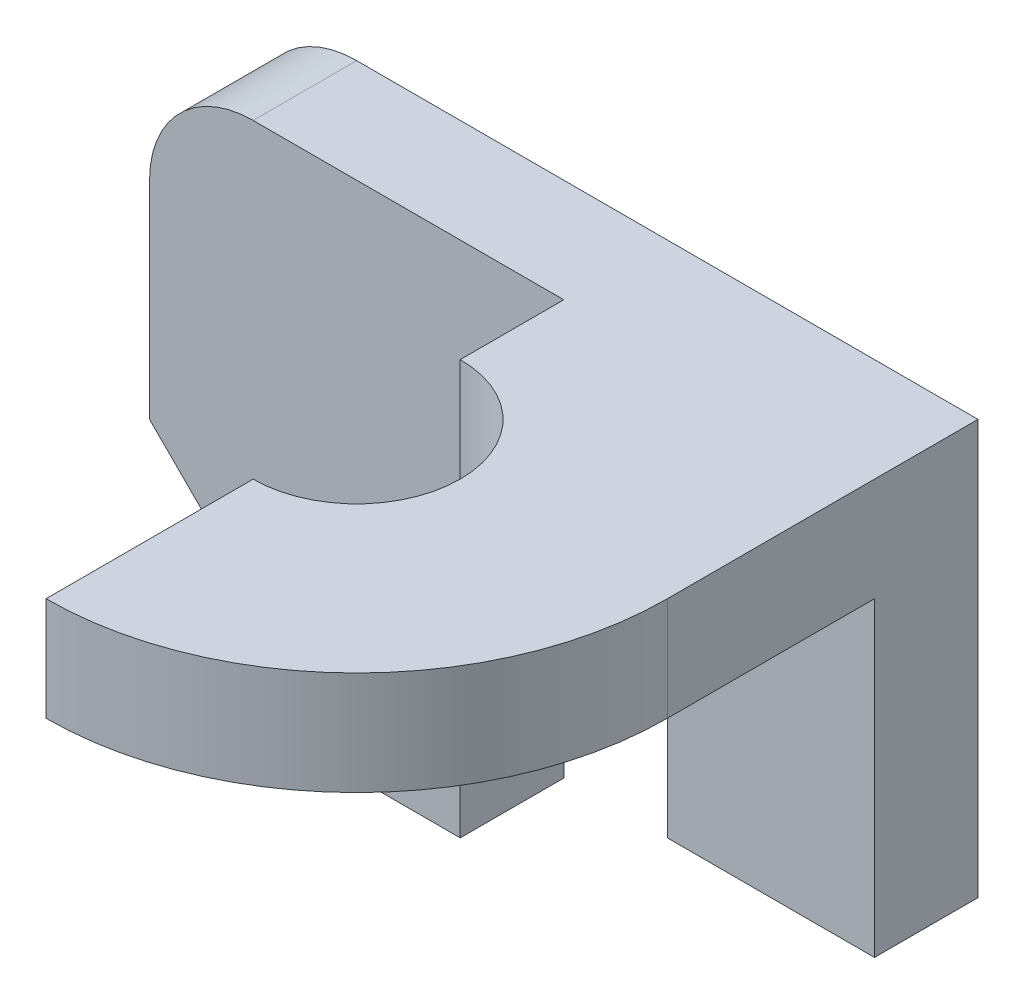
SolidWorks part; units mm, degrees
ref_plane "Front Plane" through (0, 0, 0) normal (0, 0, 1) x (1, 0, 0)
ref_plane "Top Plane" through (0, 0, 0) normal (0, 1, 0) x (1, 0, 0)
ref_plane "Right Plane" through (0, 0, 0) normal (1, 0, 0) x (0, 0, -1)
sketch "Sketch1" plane through (0, 0, 0) normal (0, 0, 1) x (1, 0, 0)
  line L0 (0, 0) -> (2, 0)
  line L1 (2, 0) -> (2, 4)
  line L2 (2, 4) -> (-4, 4)
  line L3 (-5, 3) -> (-5, 1)
  line L4 (-5, 1) -> (-3, -1)
  line L5 (-3, -1) -> (-2, -1)
  line L6 (-2, -1) -> (-2, 1)
  line L7 (0, 0) -> (0, 1)
  arc A0 (-2, 1) -> (0, 1) centre (-1, 1) cw
  arc A1 (-4, 4) -> (-5, 3) centre (-4, 3) ccw
  dimension "D1" = 2
  dimension "D2" = 4
  dimension "D3" = 6
  dimension "D4" = 1
  dimension "D5" = 1
  dimension "D6" = 2
  dimension "D7" = 2
  dimension "D8" = 2
  dimension "D9" = 1
  dimension "D10" = 2
  dimension "D11" = 1
extrude "Boss-Extrude1" add sketch "Sketch1" along normal blind 1
sketch "Sketch2" plane through (0, 4, 0) normal (0, 1, 0) x (1, 0, 0)
  line L0 (-1, -1) -> (2, -1)
  line L1 (2, -1) -> (-4, -1) construction
  line L2 (2, -1) -> (2, -3)
  line L3 (-1, -1) -> (-1, -2)
  line L4 (-1, -4) -> (-1, -6)
  arc A0 (2, -3) -> (-1, -6) centre (-1, -3) cw
  arc A1 (-1, -2) -> (-1, -4) centre (-1, -3) cw
  dimension "D5" = 1
  dimension "D1" = 3
  dimension "D2" = 2
  dimension "D3" = 5
  dimension "D4" = 1
  dimension "D6" = 2
extrude "Boss-Extrude2" add sketch "Sketch2" against normal blind 1
